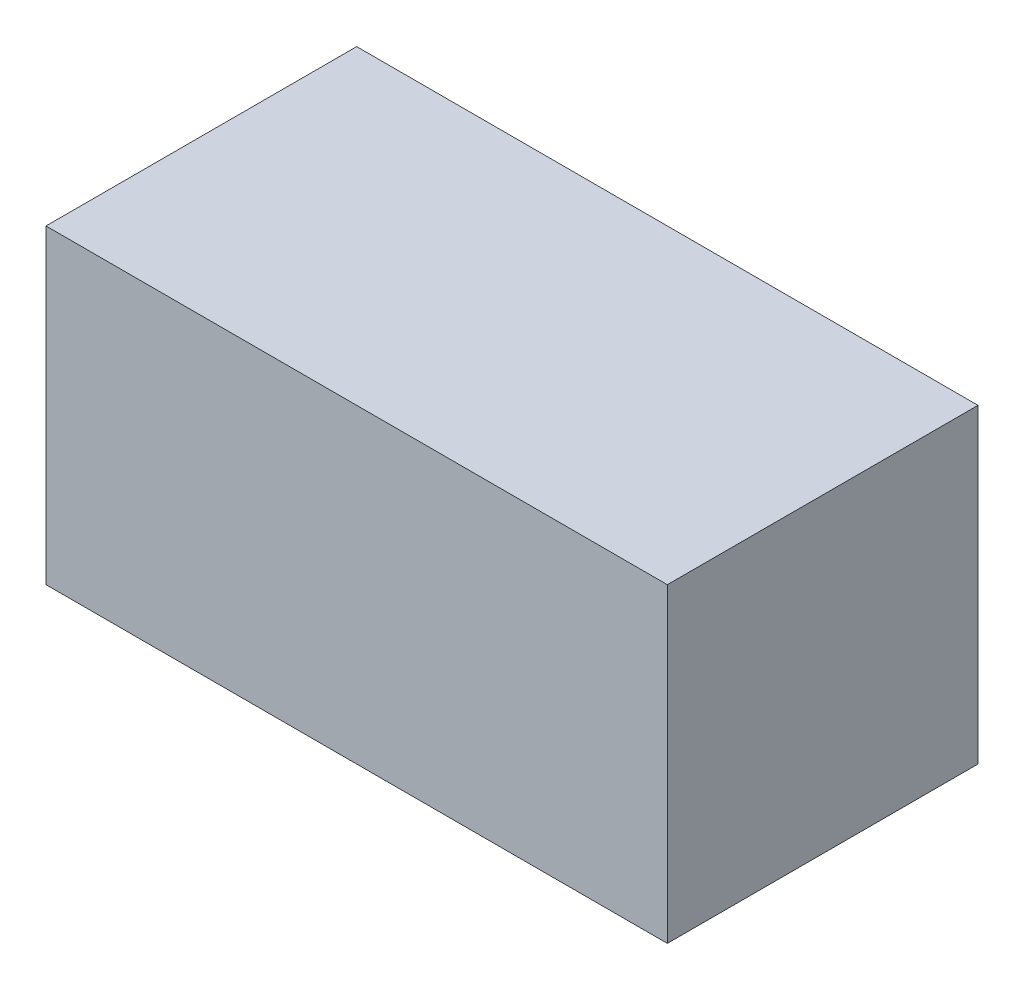
SolidWorks part; units mm, degrees
ref_plane "Alzado" through (0, 0, 0) normal (0, 0, 1) x (1, 0, 0)
ref_plane "Planta" through (0, 0, 0) normal (0, 1, 0) x (1, 0, 0)
ref_plane "Vista lateral" through (0, 0, 0) normal (1, 0, 0) x (0, 0, -1)
sketch "Croquis1" plane through (0, 0, 0) normal (0, 0, 1) x (1, 0, 0)
  line L0 (-51.5386, 30.5552) -> (-51.5386, 25.5552)
  line L1 (-51.5386, 25.5552) -> (-41.5386, 25.5552)
  line L2 (-51.5386, 30.5552) -> (-41.5386, 30.5552)
  line L3 (-41.5386, 30.5552) -> (-41.5386, 25.5552)
  dimension "D1" = 10
extrude "Saliente-Extruir1" add sketch "Croquis1" along normal blind 5
